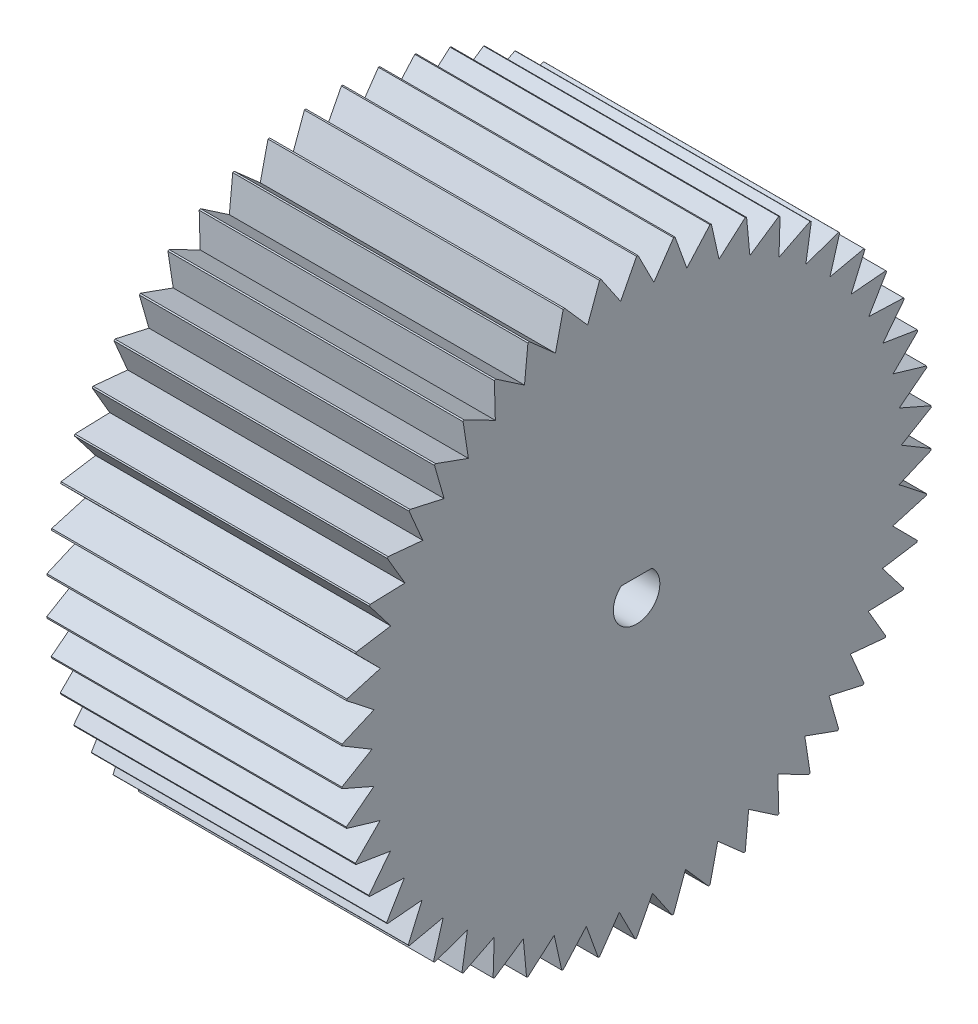
SolidWorks part; units mm, degrees
ref_plane "Front Plane" through (0, 0, 0) normal (0, 0, 1) x (1, 0, 0)
ref_plane "Top Plane" through (0, 0, 0) normal (0, 1, 0) x (1, 0, 0)
ref_plane "Right Plane" through (0, 0, 0) normal (1, 0, 0) x (0, 0, -1)
sketch "Sketch1" plane through (0, 0, 0) normal (1, 0, 0) x (0, 0, -1)
  line L0 (-3.0582, 25.2152) -> (-1.3735, 22.7329)
  line L1 (-1.3735, 22.7329) -> (0, 25.4)
  line L2 (0.1263, 25.3997) -> (1.4865, 22.7258)
  line L3 (1.4865, 22.7258) -> (3.1835, 25.1997)
  line L4 (3.3087, 25.1836) -> (4.3231, 22.3603)
  line L5 (4.3231, 22.3603) -> (6.3167, 24.602)
  line L6 (6.4389, 24.5703) -> (7.0915, 21.6421)
  line L7 (7.0915, 21.6421) -> (9.3504, 23.6163)
  line L8 (9.4676, 23.5696) -> (9.748, 20.5827)
  line L9 (9.748, 20.5827) -> (12.2365, 22.2582)
  line L10 (12.347, 22.1971) -> (12.2509, 19.1986)
  line L11 (12.2509, 19.1986) -> (14.9297, 20.549)
  line L12 (15.0317, 20.4746) -> (14.5605, 17.5118)
  line L13 (14.5605, 17.5118) -> (17.3875, 18.5158)
  line L14 (17.4793, 18.4291) -> (16.6405, 15.5488)
  line L15 (16.6405, 15.5488) -> (19.571, 16.1906)
  line L16 (19.6513, 16.0931) -> (18.4581, 13.3406)
  line L17 (18.4581, 13.3406) -> (21.4459, 13.61)
  line L18 (21.5133, 13.5032) -> (19.9845, 10.922)
  line L19 (19.9845, 10.922) -> (22.9826, 10.8148)
  line L20 (23.0361, 10.7004) -> (21.1958, 8.3311)
  line L21 (21.1958, 8.3311) -> (24.1568, 7.849)
  line L22 (24.1956, 7.7289) -> (22.0729, 5.6089)
  line L23 (22.0729, 5.6089) -> (24.9501, 4.7595)
  line L24 (24.9734, 4.6354) -> (22.6018, 2.7982)
  line L25 (22.6018, 2.7982) -> (25.3499, 1.5949)
  line L26 (25.3575, 1.4689) -> (22.7743, -0.0566)
  line L27 (22.7743, -0.0566) -> (25.3499, -1.5949)
  line L28 (25.3416, -1.7209) -> (22.5876, -2.9105)
  line L29 (22.5876, -2.9105) -> (24.9501, -4.7595)
  line L30 (24.9261, -4.8834) -> (22.0447, -5.7186)
  line L31 (22.0447, -5.7186) -> (24.1568, -7.849)
  line L32 (24.1175, -7.969) -> (21.1542, -8.4364)
  line L33 (21.1542, -8.4364) -> (22.9826, -10.8148)
  line L34 (22.9286, -10.9289) -> (19.93, -11.0212)
  line L35 (19.93, -11.0212) -> (21.4459, -13.61)
  line L36 (21.378, -13.7164) -> (18.3915, -13.4322)
  line L37 (18.3915, -13.4322) -> (19.571, -16.1906)
  line L38 (19.4903, -16.2877) -> (16.563, -15.6313)
  line L39 (16.563, -15.6313) -> (17.3875, -18.5158)
  line L40 (17.2952, -18.602) -> (14.4733, -17.584)
  line L41 (14.4733, -17.584) -> (14.9297, -20.549)
  line L42 (14.8274, -20.623) -> (12.1553, -19.2593)
  line L43 (12.1553, -19.2593) -> (12.2365, -22.2582)
  line L44 (12.1258, -22.3187) -> (9.6456, -20.6309)
  line L45 (9.6456, -20.6309) -> (9.3504, -23.6163)
  line L46 (9.2329, -23.6625) -> (6.9838, -21.6771)
  line L47 (6.9838, -21.6771) -> (6.3167, -24.602)
  line L48 (6.1944, -24.6331) -> (4.2119, -22.3815)
  line L49 (4.2119, -22.3815) -> (3.1835, -25.1997)
  line L50 (3.0582, -25.2152) -> (1.3735, -22.7329)
  line L51 (1.3735, -22.7329) -> (0, -25.4)
  line L52 (-0.1263, -25.3997) -> (-1.4865, -22.7258)
  line L53 (-1.4865, -22.7258) -> (-3.1835, -25.1997)
  line L54 (-3.3087, -25.1836) -> (-4.3231, -22.3603)
  line L55 (-4.3231, -22.3603) -> (-6.3167, -24.602)
  line L56 (-6.4389, -24.5703) -> (-7.0915, -21.6421)
  line L57 (-7.0915, -21.6421) -> (-9.3504, -23.6163)
  line L58 (-9.4676, -23.5696) -> (-9.748, -20.5827)
  line L59 (-9.748, -20.5827) -> (-12.2365, -22.2582)
  line L60 (-12.347, -22.1971) -> (-12.2509, -19.1986)
  line L61 (-12.2509, -19.1986) -> (-14.9297, -20.549)
  line L62 (-15.0317, -20.4746) -> (-14.5605, -17.5118)
  line L63 (-14.5605, -17.5118) -> (-17.3875, -18.5158)
  line L64 (-17.4793, -18.4291) -> (-16.6405, -15.5488)
  line L65 (-16.6405, -15.5488) -> (-19.571, -16.1906)
  line L66 (-19.6513, -16.0931) -> (-18.4581, -13.3406)
  line L67 (-18.4581, -13.3406) -> (-21.4459, -13.61)
  line L68 (-21.5133, -13.5032) -> (-19.9845, -10.922)
  line L69 (-19.9845, -10.922) -> (-22.9826, -10.8148)
  line L70 (-23.0361, -10.7004) -> (-21.1958, -8.3311)
  line L71 (-21.1958, -8.3311) -> (-24.1568, -7.849)
  line L72 (-24.1956, -7.7289) -> (-22.0729, -5.6089)
  line L73 (-22.0729, -5.6089) -> (-24.9501, -4.7595)
  line L74 (-24.9734, -4.6354) -> (-22.6018, -2.7982)
  line L75 (-22.6018, -2.7982) -> (-25.3499, -1.5949)
  line L76 (-25.3575, -1.4689) -> (-22.7743, 0.0566)
  line L77 (-22.7743, 0.0566) -> (-25.3499, 1.5949)
  line L78 (-25.3416, 1.7209) -> (-22.5876, 2.9105)
  line L79 (-22.5876, 2.9105) -> (-24.9501, 4.7595)
  line L80 (-24.9261, 4.8834) -> (-22.0447, 5.7186)
  line L81 (-22.0447, 5.7186) -> (-24.1568, 7.849)
  line L82 (-24.1175, 7.969) -> (-21.1542, 8.4364)
  line L83 (-21.1542, 8.4364) -> (-22.9826, 10.8148)
  line L84 (-22.9286, 10.9289) -> (-19.93, 11.0212)
  line L85 (-19.93, 11.0212) -> (-21.4459, 13.61)
  line L86 (-21.378, 13.7164) -> (-18.3915, 13.4322)
  line L87 (-18.3915, 13.4322) -> (-19.571, 16.1906)
  line L88 (-19.4903, 16.2877) -> (-16.563, 15.6313)
  line L89 (-16.563, 15.6313) -> (-17.3875, 18.5158)
  line L90 (-17.2952, 18.602) -> (-14.4733, 17.584)
  line L91 (-14.4733, 17.584) -> (-14.9297, 20.549)
  line L92 (-14.8274, 20.623) -> (-12.1553, 19.2593)
  line L93 (-12.1553, 19.2593) -> (-12.2365, 22.2582)
  line L94 (-12.1258, 22.3187) -> (-9.6456, 20.6309)
  line L95 (-9.6456, 20.6309) -> (-9.3504, 23.6163)
  line L96 (-9.2329, 23.6625) -> (-6.9838, 21.6771)
  line L97 (-6.9838, 21.6771) -> (-6.3167, 24.602)
  line L98 (-6.1944, 24.6331) -> (-4.2119, 22.3815)
  line L99 (-4.2119, 22.3815) -> (-3.1835, 25.1997)
  line L100 (-1.3229, 1.5) -> (1.3229, 1.5)
  arc A0 (-3.0582, 25.2152) -> (-3.1835, 25.1997) centre (0, 0) ccw
  arc A1 (-6.1944, 24.6331) -> (-6.3167, 24.602) centre (0, 0) ccw
  arc A2 (-9.2329, 23.6625) -> (-9.3504, 23.6163) centre (0, 0) ccw
  arc A3 (-12.1258, 22.3187) -> (-12.2365, 22.2582) centre (0, 0) ccw
  arc A4 (-14.8274, 20.623) -> (-14.9297, 20.549) centre (0, 0) ccw
  arc A5 (-17.2952, 18.602) -> (-17.3875, 18.5158) centre (0, 0) ccw
  arc A6 (-19.4903, 16.2877) -> (-19.571, 16.1906) centre (0, 0) ccw
  arc A7 (-21.378, 13.7164) -> (-21.4459, 13.61) centre (0, 0) ccw
  arc A8 (-22.9286, 10.9289) -> (-22.9826, 10.8148) centre (0, 0) ccw
  arc A9 (-24.1175, 7.969) -> (-24.1568, 7.849) centre (0, 0) ccw
  arc A10 (-24.9261, 4.8834) -> (-24.9501, 4.7595) centre (0, 0) ccw
  arc A11 (-25.3416, 1.7209) -> (-25.3499, 1.5949) centre (0, 0) ccw
  arc A12 (-25.3575, -1.4689) -> (-25.3499, -1.5949) centre (0, 0) ccw
  arc A13 (0.1263, 25.3997) -> (0, 25.4) centre (0, 0) ccw
  arc A14 (3.3087, 25.1836) -> (3.1835, 25.1997) centre (0, 0) ccw
  arc A15 (6.4389, 24.5703) -> (6.3167, 24.602) centre (0, 0) ccw
  arc A16 (9.4676, 23.5696) -> (9.3504, 23.6163) centre (0, 0) ccw
  arc A17 (12.347, 22.1971) -> (12.2365, 22.2582) centre (0, 0) ccw
  arc A18 (15.0317, 20.4746) -> (14.9297, 20.549) centre (0, 0) ccw
  arc A19 (17.4793, 18.4291) -> (17.3875, 18.5158) centre (0, 0) ccw
  arc A20 (19.6513, 16.0931) -> (19.571, 16.1906) centre (0, 0) ccw
  arc A21 (21.5133, 13.5032) -> (21.4459, 13.61) centre (0, 0) ccw
  arc A22 (23.0361, 10.7004) -> (22.9826, 10.8148) centre (0, 0) ccw
  arc A23 (24.1956, 7.7289) -> (24.1568, 7.849) centre (0, 0) ccw
  arc A24 (24.9734, 4.6354) -> (24.9501, 4.7595) centre (0, 0) ccw
  arc A25 (25.3575, 1.4689) -> (25.3499, 1.5949) centre (0, 0) ccw
  arc A26 (25.3416, -1.7209) -> (25.3499, -1.5949) centre (0, 0) ccw
  arc A27 (24.9261, -4.8834) -> (24.9501, -4.7595) centre (0, 0) ccw
  arc A28 (24.1175, -7.969) -> (24.1568, -7.849) centre (0, 0) ccw
  arc A29 (22.9286, -10.9289) -> (22.9826, -10.8148) centre (0, 0) ccw
  arc A30 (21.378, -13.7164) -> (21.4459, -13.61) centre (0, 0) ccw
  arc A31 (19.4903, -16.2877) -> (19.571, -16.1906) centre (0, 0) ccw
  arc A32 (17.2952, -18.602) -> (17.3875, -18.5158) centre (0, 0) ccw
  arc A33 (14.8274, -20.623) -> (14.9297, -20.549) centre (0, 0) ccw
  arc A34 (12.1258, -22.3187) -> (12.2365, -22.2582) centre (0, 0) ccw
  arc A35 (9.2329, -23.6625) -> (9.3504, -23.6163) centre (0, 0) ccw
  arc A36 (6.1944, -24.6331) -> (6.3167, -24.602) centre (0, 0) ccw
  arc A37 (3.0582, -25.2152) -> (3.1835, -25.1997) centre (0, 0) ccw
  arc A38 (-0.1263, -25.3997) -> (0, -25.4) centre (0, 0) ccw
  arc A39 (-3.3087, -25.1836) -> (-3.1835, -25.1997) centre (0, 0) ccw
  arc A40 (-6.4389, -24.5703) -> (-6.3167, -24.602) centre (0, 0) ccw
  arc A41 (-9.4676, -23.5696) -> (-9.3504, -23.6163) centre (0, 0) ccw
  arc A42 (-12.347, -22.1971) -> (-12.2365, -22.2582) centre (0, 0) ccw
  arc A43 (-15.0317, -20.4746) -> (-14.9297, -20.549) centre (0, 0) ccw
  arc A44 (-17.4793, -18.4291) -> (-17.3875, -18.5158) centre (0, 0) ccw
  arc A45 (-19.6513, -16.0931) -> (-19.571, -16.1906) centre (0, 0) ccw
  arc A46 (-21.5133, -13.5032) -> (-21.4459, -13.61) centre (0, 0) ccw
  arc A47 (-23.0361, -10.7004) -> (-22.9826, -10.8148) centre (0, 0) ccw
  arc A48 (-24.1956, -7.7289) -> (-24.1568, -7.849) centre (0, 0) ccw
  arc A49 (-24.9734, -4.6354) -> (-24.9501, -4.7595) centre (0, 0) ccw
  arc A50 (-1.3229, 1.5) -> (1.3229, 1.5) centre (0, 0) ccw
  point P156 (0, 0)
  dimension "D1" = 50.8
  dimension "D5" = 4
  dimension "D2" = 3
  dimension "D3" = 3
  dimension "D6" = 1.5
  dimension "D4" = 50
extrude "Boss-Extrude1" add sketch "Sketch1" along normal blind 25.4
